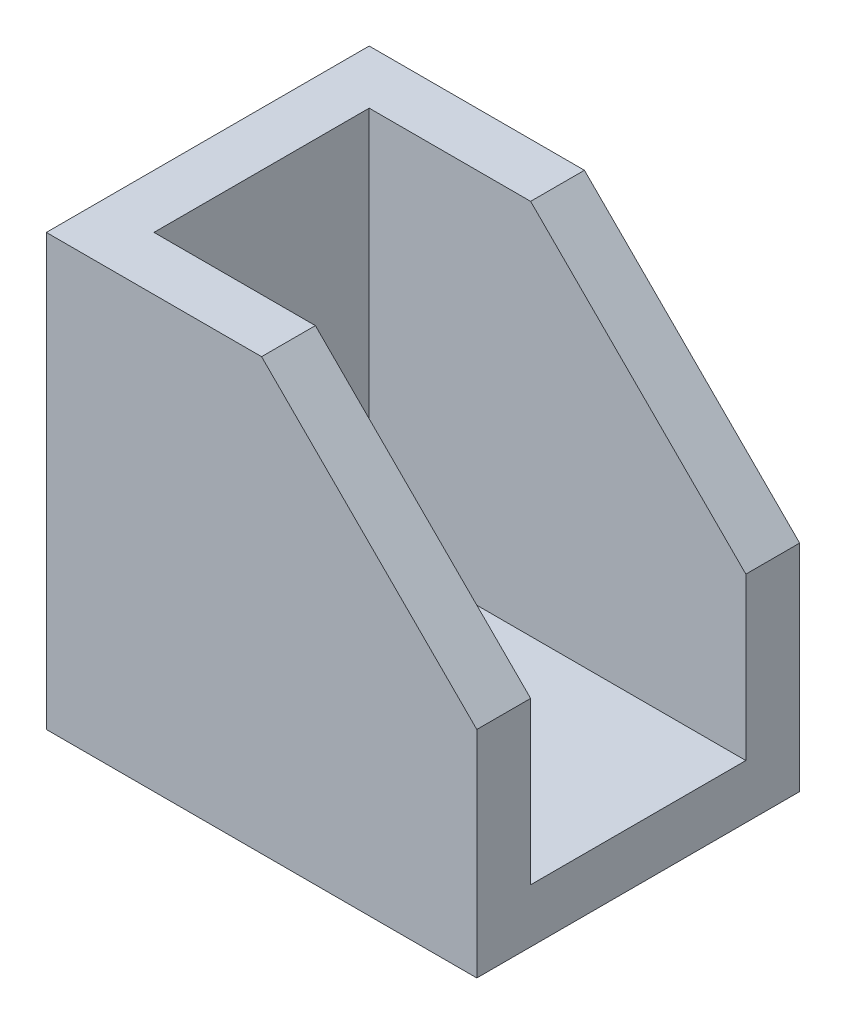
SolidWorks part; units mm, degrees
ref_plane "Front Plane" through (0, 0, 0) normal (0, 0, 1) x (1, 0, 0)
ref_plane "Top Plane" through (0, 0, 0) normal (0, 1, 0) x (1, 0, 0)
ref_plane "Right Plane" through (0, 0, 0) normal (1, 0, 0) x (0, 0, -1)
sketch "Sketch1" plane through (0, 0, 0) normal (0, 0, 1) x (1, 0, 0)
  line L0 (0, 0) -> (0, 20)
  line L1 (0, 20) -> (10, 20)
  line L2 (10, 20) -> (20, 10)
  line L3 (20, 10) -> (20, 0)
  line L4 (20, 0) -> (0, 0)
  dimension "D1" = 20
  dimension "D2" = 20
  dimension "D3" = 10
  dimension "D4" = 10
extrude "Boss-Extrude1" add sketch "Sketch1" along normal blind 15
sketch "Sketch2" plane through (20, 0, 0) normal (1, 0, 0) x (0, 0, -1)
  line L0 (-7.5, 0) -> (-7.5, 10) construction
  line L1 (-15, 0) -> (0, 0) construction
  line L2 (-15, 10) -> (0, 10) construction
  line L3 (-7.5, 5) -> (0, 5) construction
  line L4 (0, 0) -> (0, 10) construction
  line L5 (-15, 20) -> (0, 20) construction
  line L6 (-2.5, 2.5) -> (-12.5, 2.5)
  line L7 (-2.5, 2.5) -> (-2.5, 17.5)
  line L8 (-2.5, 17.5) -> (-12.5, 17.5)
  line L9 (-12.5, 2.5) -> (-12.5, 17.5)
  line L10 (-2.5, 2.5) -> (-12.5, 17.5) construction
  line L11 (-2.5, 17.5) -> (-12.5, 2.5) construction
  line L12 (-12.5, 17.5) -> (-2.5, 17.5)
  line L13 (-12.5, 17.5) -> (-12.5, 20)
  line L14 (-12.5, 20) -> (-2.5, 20)
  line L15 (-2.5, 17.5) -> (-2.5, 20)
  line M2 (0, 10) -> (-15, 10)
  dimension "D1" = 10
  dimension "D2" = 15
extrude "Cut-Extrude2" cut sketch "Sketch2" against normal blind 17.5 contours L8 L15 L14 L13 | L9 L7 L8 M2 | L9 L6 L7 M2
